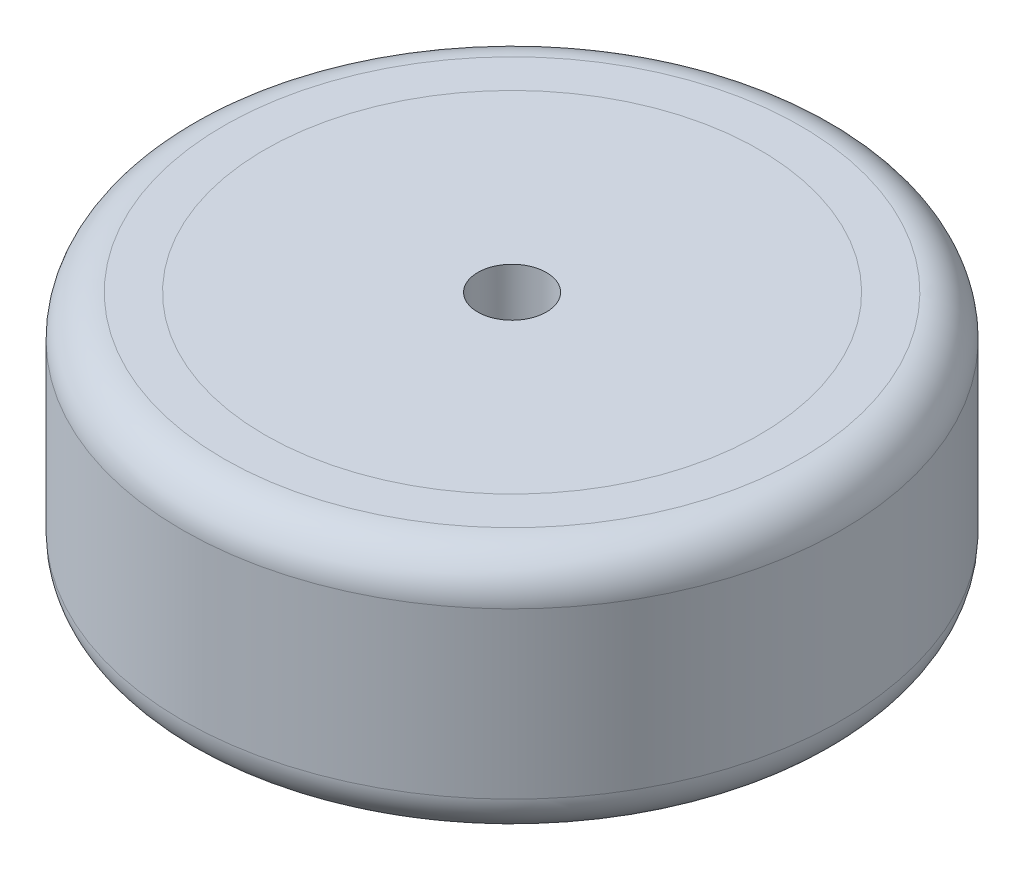
SolidWorks part; units mm, degrees
ref_plane "Front Plane" through (0, 0, 0) normal (0, 0, 1) x (1, 0, 0)
ref_plane "Top Plane" through (0, 0, 0) normal (0, 1, 0) x (1, 0, 0)
ref_plane "Right Plane" through (0, 0, 0) normal (1, 0, 0) x (0, 0, -1)
sketch "Sketch1" plane through (0, 0, 0) normal (0, 1, 0) x (1, 0, 0)
  circle A0 centre (0, 0) radius 24
  dimension "D1" = 48
extrude "Boss-Extrude1" add sketch "Sketch1" along normal blind 18
sketch "Sketch2" plane through (0, 18, 0) normal (0, 1, 0) x (1, 0, 0)
  circle A0 centre (0, 0) radius 18
  circle A1 centre (0, 0) radius 24 construction
  dimension "D1" = 6
extrude "Cut-Extrude1" cut sketch "Sketch2" against normal blind 5
sketch "Sketch3" plane through (0, 0, 0) normal (0, -1, 0) x (1, 0, 0)
  circle A0 centre (0, 0) radius 18
  circle A1 centre (0, 0) radius 24 construction
  dimension "D1" = 6
extrude "Cut-Extrude2" cut sketch "Sketch3" against normal blind 5
sketch "Sketch4" plane through (0, 13, 0) normal (0, 1, 0) x (1, 0, 0)
  circle A0 centre (0, 0) radius 18
extrude "Boss-Extrude2" add sketch "Sketch4" along normal blind 5 separate body
sketch "Sketch5" plane through (0, 5, 0) normal (0, -1, 0) x (1, 0, 0)
  circle A0 centre (0, 0) radius 18
extrude "Boss-Extrude3" add sketch "Sketch5" along normal blind 5 separate body
sketch "Sketch6" plane through (0, 0, 0) normal (0, -1, 0) x (-1, 0, 0)
  circle A0 centre (0, 0) radius 2.5
  dimension "D1" = 5
extrude "Cut-Extrude3" cut sketch "Sketch6" against normal through all
fillet "Fillet1" radius 3 2 edges at (0, 18, 24) (0, 0, 24)
